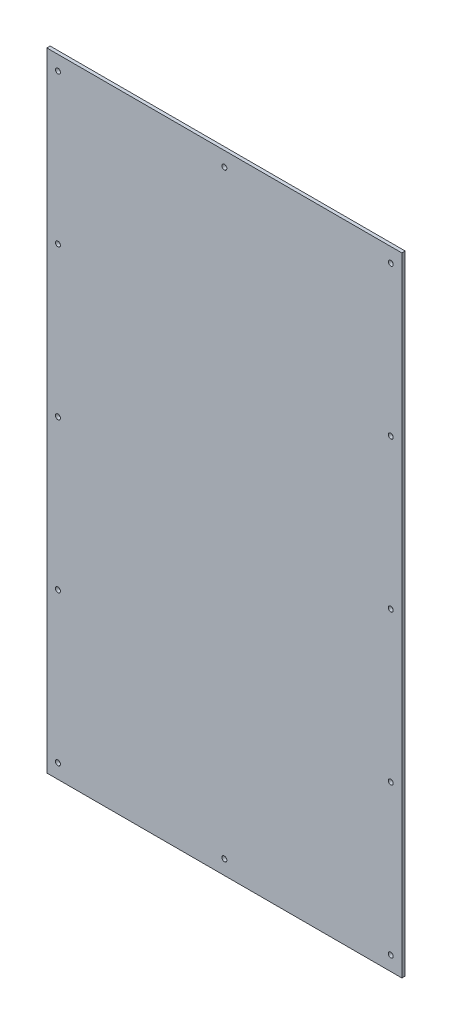
SolidWorks part; units mm, degrees
ref_plane "Спереди" through (0, 0, 0) normal (0, 0, 1) x (1, 0, 0)
ref_plane "Сверху" through (0, 0, 0) normal (0, 1, 0) x (1, 0, 0)
ref_plane "Справа" through (0, 0, 0) normal (1, 0, 0) x (0, 0, -1)
sketch "Эскиз1" plane through (0, 0, 0) normal (0, 0, 1) x (1, 0, 0)
  line L0 (0, 0) -> (320, 0)
  line L1 (0, 0) -> (0, 566)
  line L2 (320, 0) -> (320, 566)
  line L3 (0, 566) -> (320, 566)
  line L4 (10, 553) -> (310, 553) construction
  line L5 (10, 553) -> (10, 13) construction
  line L6 (310, 553) -> (310, 13) construction
  line L7 (10, 13) -> (310, 13) construction
  line L8 (160, 553) -> (160, 13) construction
  circle A0 centre (10, 553) radius 2.25
  circle A1 centre (10, 418) radius 2.25
  circle A2 centre (10, 283) radius 2.25
  circle A3 centre (10, 148) radius 2.25
  circle A4 centre (10, 13) radius 2.25
  circle A5 centre (160, 553) radius 2.25
  circle A6 centre (160, 13) radius 2.25
  circle A7 centre (310, 553) radius 2.25
  circle A8 centre (310, 418) radius 2.25
  circle A9 centre (310, 283) radius 2.25
  circle A10 centre (310, 148) radius 2.25
  circle A11 centre (310, 13) radius 2.25
  dimension "D7" = 4.5
  dimension "D9" = 135
  dimension "D10" = 4.5
  dimension "D12" = 135
  dimension "D13" = 4.5
  dimension "D22" = 4.5
  dimension "D1" = 566
  dimension "D2" = 320
  dimension "D3" = 10
  dimension "D4" = 13
  dimension "D5" = 10
  dimension "D6" = 13
  dimension "D8" = 5
  dimension "D11" = 5
extrude "Бобышка-Вытянуть1" add sketch "Эскиз1" along normal blind 3
